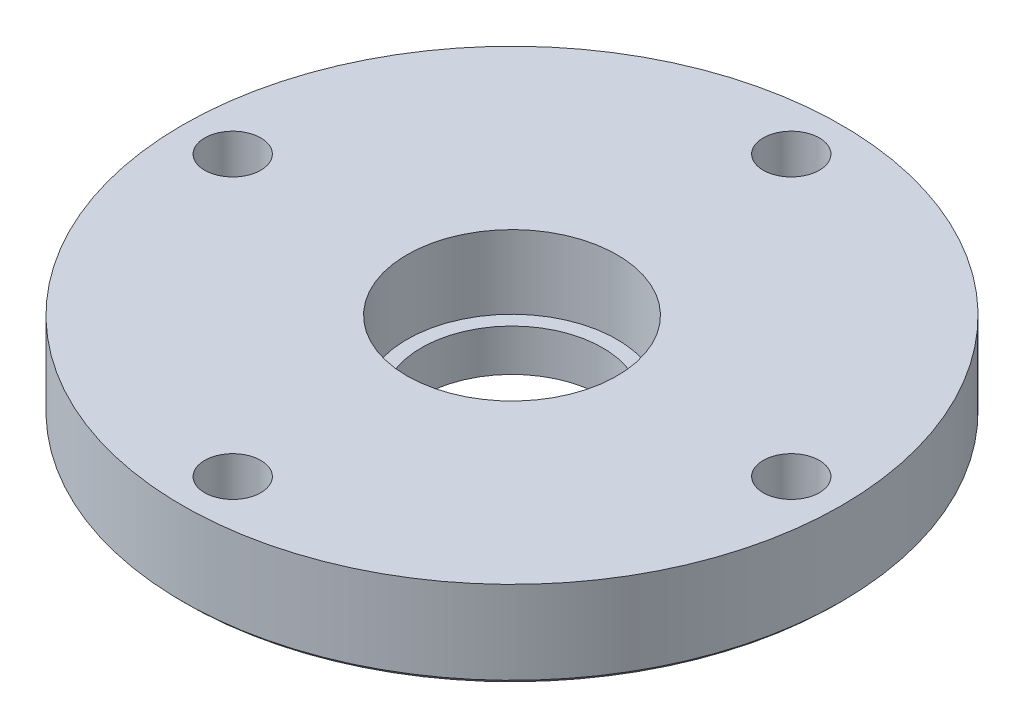
SolidWorks part; units mm, degrees
ref_plane "Front Plane" through (0, 0, 0) normal (0, 0, 1) x (1, 0, 0)
ref_plane "Top Plane" through (0, 0, 0) normal (0, 1, 0) x (1, 0, 0)
ref_plane "Right Plane" through (0, 0, 0) normal (1, 0, 0) x (0, 0, -1)
ref_plane "Plane1" through (0, 0, 0) normal (0, 0, -1) x (-1, 0, 0)
sketch "Sketch1" plane through (0, 0, 0) normal (0, 0, -1) x (-1, 0, 0)
  line L0 (-29.591, 0) -> (0, 0)
  line L1 (0, 0) -> (0, 7.9375)
  line L2 (0, 7.9375) -> (-29.972, 7.9375)
  line L3 (-29.972, 7.9375) -> (-29.972, 0.381)
  line L4 (-29.972, 0.381) -> (-29.591, 0)
  line L5 (0, 0) -> (0, 7.9375) construction
revolve "Revolve1" add sketch "Sketch1" angle 360 about L5
sketch "Sketch2" plane through (0, 0, 0) normal (0, -1, 0) x (1, 0, 0)
  circle A0 centre (0, 0) radius 9.506
extrude "Boss-Extrude1" add sketch "Sketch2" along normal blind 2.159
sketch "Sketch3" plane through (0, -2.159, 0) normal (0, -1, 0) x (1, 0, 0)
  circle A0 centre (0, 0) radius 9.506
extrude "Boss-Extrude2" add sketch "Sketch3" along normal blind 0.381 draft 45
sketch "Sketch4" plane through (0, 7.9375, 0) normal (0, 1, 0) x (-1, 0, 0)
  line L0 (0.9525, 21.0583) -> (0.9525, 11.3902)
  line L1 (11.3902, 0.9525) -> (21.0583, 0.9525)
  arc A0 (4.0969, 27.1243) -> (0.9525, 21.0583) centre (0, 25.4) cw
  arc A1 (0.9525, 11.3902) -> (11.3902, 0.9525) centre (0, 0) cw
  arc A2 (21.0583, 0.9525) -> (27.1243, 4.0969) centre (25.4, 0) cw
  arc A3 (27.1243, 4.0969) -> (4.0969, 27.1243) centre (0, 0) ccw
sketch "Sketch5" plane through (0, 7.9375, 0) normal (0, 1, 0) x (-1, 0, 0)
  line L0 (-0.9525, -21.0583) -> (-0.9525, -11.3902)
  line L1 (-11.3902, -0.9525) -> (-21.0583, -0.9525)
  arc A0 (-4.0969, -27.1243) -> (-0.9525, -21.0583) centre (0, -25.4) cw
  arc A1 (-0.9525, -11.3902) -> (-11.3902, -0.9525) centre (0, 0) cw
  arc A2 (-21.0583, -0.9525) -> (-27.1243, -4.0969) centre (-25.4, 0) cw
  arc A3 (-27.1243, -4.0969) -> (-4.0969, -27.1243) centre (0, 0) ccw
sketch "Sketch6" plane through (0, 7.9375, 0) normal (0, 1, 0) x (-1, 0, 0)
  line L0 (-21.0583, 0.9525) -> (-11.3902, 0.9525)
  line L1 (-0.9525, 11.3902) -> (-0.9525, 21.0583)
  arc A0 (-4.0969, 27.1243) -> (-27.1243, 4.0969) centre (0, 0) ccw
  arc A1 (-27.1243, 4.0969) -> (-21.0583, 0.9525) centre (-25.4, 0) cw
  arc A2 (-11.3902, 0.9525) -> (-0.9525, 11.3902) centre (0, 0) cw
  arc A3 (-0.9525, 21.0583) -> (-4.0969, 27.1243) centre (0, 25.4) cw
sketch "Sketch7" plane through (0, 7.9375, 0) normal (0, 1, 0) x (-1, 0, 0)
  line L0 (21.0583, -0.9525) -> (11.3902, -0.9525)
  line L1 (0.9525, -11.3902) -> (0.9525, -21.0583)
  arc A0 (27.1243, -4.0969) -> (21.0583, -0.9525) centre (25.4, 0) cw
  arc A1 (11.3902, -0.9525) -> (0.9525, -11.3902) centre (0, 0) cw
  arc A2 (0.9525, -21.0583) -> (4.0969, -27.1243) centre (0, -25.4) cw
  arc A3 (4.0969, -27.1243) -> (27.1243, -4.0969) centre (0, 0) ccw
hole_wizard "Hole1" positions "Sketch9" profile "Sketch8" legacy
sketch "Sketch9" plane through (0, 0, 0) normal (0, -1, 0) x (-1, 0, 0)
  point P0 (0, -25.4)
sketch "Sketch8" plane through (0, 0, 25.4) normal (1, 0, 0) x (0, 0, -1)
  line L0 (0, 0) -> (0, 7.9375)
  line L1 (0, 7.9375) -> (2.5527, 7.9375)
  line L2 (2.5527, 7.9375) -> (2.5527, 0)
  line L3 (2.5527, 0) -> (0, 0)
  line L4 (0, 110) -> (0, -10) construction
  dimension "Diameter" = 5.1054
  dimension "Depth" = 7.9375
hole_wizard "Hole2" positions "Sketch11" profile "Sketch10" legacy
sketch "Sketch11" plane through (0, 7.9375, 0) normal (0, 1, 0) x (1, 0, 0)
  point P0 (0, 25.4)
  point P1 (25.4, 0)
  point P2 (-25.4, 0)
sketch "Sketch10" plane through (0, 7.9375, -25.4) normal (1, 0, 0) x (0, 0, 1)
  line L0 (0, 0) -> (0, 10.4775)
  line L1 (0, 10.4775) -> (2.5527, 10.4775)
  line L2 (2.5527, 10.4775) -> (2.5527, 0)
  line L3 (2.5527, 0) -> (0, 0)
  line L4 (0, 110) -> (0, -10) construction
  dimension "Diameter" = 5.1054
  dimension "Depth" = 10.4775
hole_wizard "CBORE for M14 Hex Head Bolt1" positions "Sketch13" profile "Sketch12" counterbore size "M14" standard "ANSI Metric"
sketch "Sketch13" plane through (0, 7.9375, 0) normal (0, 1, 0) x (1, 0, 0)
  point P0 (0, 0)
sketch "Sketch12" plane through (0, 7.9375, 0) normal (1, 0, 0) x (0, 0, 1)
  line L0 (0, 0) -> (0, 10.4775)
  line L1 (0, 10.4775) -> (8.236, 10.4775)
  line L3 (8.236, 10.4775) -> (8.236, 6.6675)
  line L4 (8.236, 6.6675) -> (9.5504, 6.6675)
  line L5 (9.5504, 6.6675) -> (9.5504, 0)
  line L7 (9.5504, 0) -> (0, 0)
  line L11 (0, -6.35) -> (0, 107.95) construction
  dimension "Thru Hole Dia." = 16.4719
  dimension "Thru Hole Depth" = 10.4775
  dimension "C'Bore Dia." = 19.1008
  dimension "C'Bore Depth" = 6.6675
